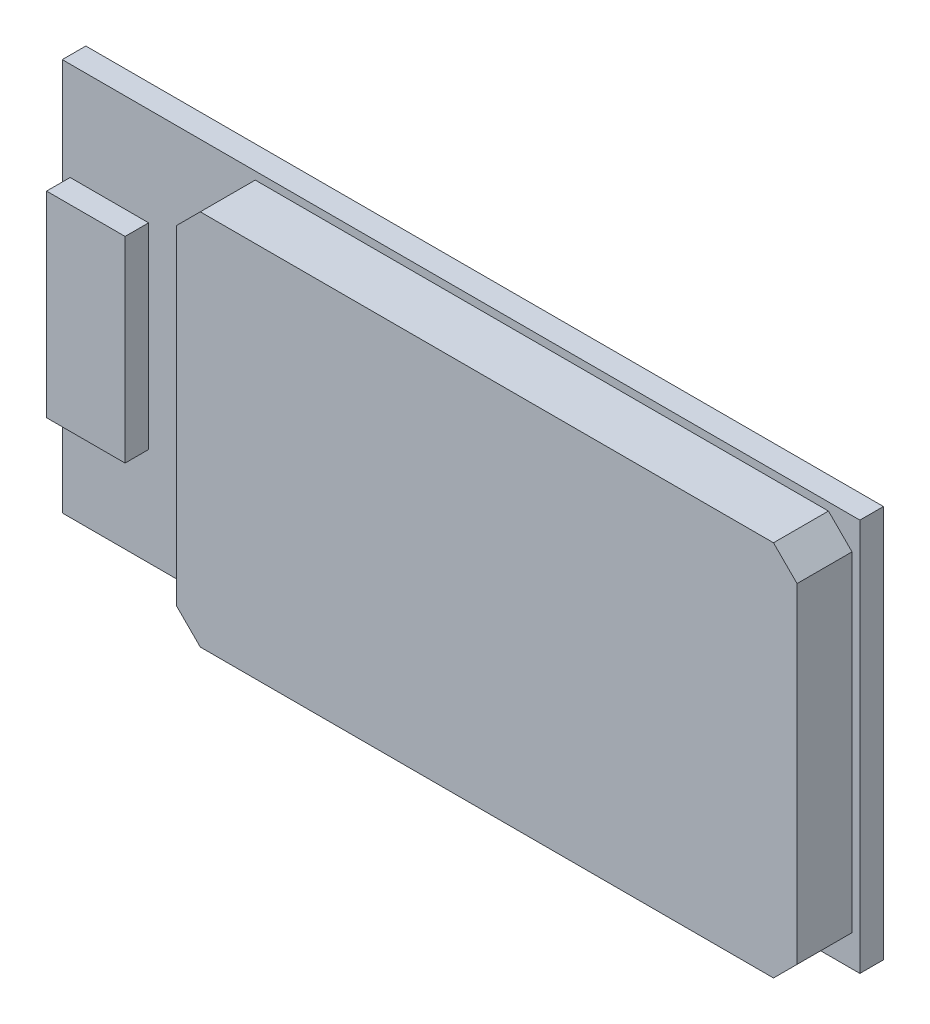
SolidWorks part; units mm, degrees
ref_plane "Front Plane" through (0, 0, 0) normal (0, 0, 1) x (1, 0, 0)
ref_plane "Top Plane" through (0, 0, 0) normal (0, 1, 0) x (1, 0, 0)
ref_plane "Right Plane" through (0, 0, 0) normal (1, 0, 0) x (0, 0, -1)
sketch "Sketch1" plane through (0, 0, 0) normal (0, 0, 1) x (1, 0, 0)
  line L1 (0, 0) -> (25.8, 0)
  line L2 (0, 0) -> (0, 12.7)
  line L3 (0, 12.7) -> (25.8, 12.7)
  line L4 (25.8, 0) -> (25.8, 12.7)
  dimension "D1" = 12.7
  dimension "D2" = 25.8
extrude "Boss-Extrude1" add sketch "Sketch1" along normal blind 0.762
sketch "Sketch2" plane through (0, 0, 0.762) normal (0, 0, 1) x (1, 0, 0)
  line L0 (25.8, 12.7) -> (0, 12.7) construction
  line L1 (5.48, 12.446) -> (25.546, 12.446)
  line L2 (5.48, 12.446) -> (5.48, 0.254)
  line L3 (5.48, 0.254) -> (25.546, 0.254)
  line L4 (25.546, 12.446) -> (25.546, 0.254)
  line L5 (25.8, 0) -> (25.8, 12.7) construction
  dimension "D1" = 0.254
  dimension "D2" = 0.254
  dimension "D3" = 20.066
  dimension "D4" = 12.192
extrude "Boss-Extrude2" add sketch "Sketch2" along normal blind 1.778
chamfer "Chamfer1" distance 0.762 angle 45 4 edges at (25.546, 12.446, 1.651) (25.546, 0.254, 1.651) (5.48, 12.446, 1.651) (5.48, 0.254, 1.651)
sketch "Sketch3" plane through (0, 0, 0.762) normal (0, 0, 1) x (1, 0, 0)
  line L0 (0, 12.7) -> (0, 0) construction
  line L1 (0.254, 9.525) -> (2.794, 9.525)
  line L2 (0.254, 9.525) -> (0.254, 3.175)
  line L3 (0.254, 3.175) -> (2.794, 3.175)
  line L4 (2.794, 9.525) -> (2.794, 3.175)
  line L5 (0.254, 6.35) -> (0, 6.35) construction
  dimension "D1" = 0.254
  dimension "D2" = 6.35
  dimension "D3" = 2.54
extrude "Boss-Extrude3" add sketch "Sketch3" along normal blind 0.762
